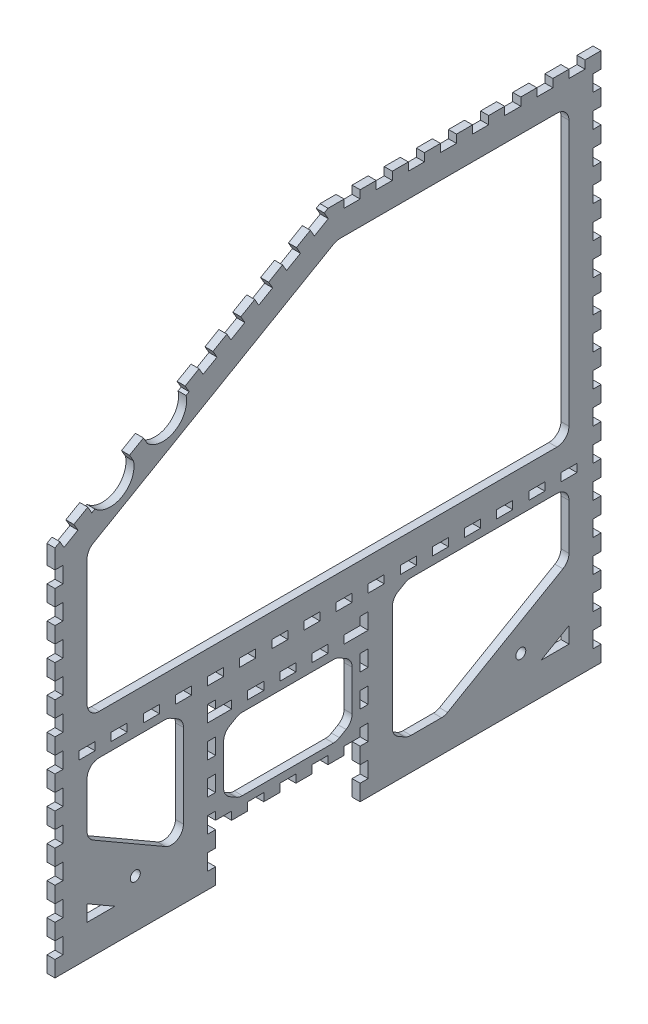
SolidWorks part; units mm, degrees
material "Pine"
ref_plane "Front Plane" through (0, 0, 0) normal (0, 0, 1) x (1, 0, 0)
ref_plane "Top Plane" through (0, 0, 0) normal (0, 1, 0) x (1, 0, 0)
ref_plane "Right Plane" through (0, 0, 0) normal (1, 0, 0) x (0, 0, -1)
sketch "Sketch2" plane through (0, 0, 0) normal (1, 0, 0) x (0, 0, -1)
  line L0 (0, 0) -> (0, 294.4501)
  line L1 (0, 294.4501) -> (215.9, 419.1)
  line L2 (215.9, 419.1) -> (431.8, 419.1)
  line L3 (431.8, 419.1) -> (431.8, 0)
  line L4 (431.8, 0) -> (241.3, 0)
  line L5 (241.3, 0) -> (241.3, 38.1)
  line L6 (241.3, 38.1) -> (127, 38.1)
  line L7 (127, 38.1) -> (127, 0)
  line L8 (127, 0) -> (0, 0)
  dimension "D1" = 431.8
  dimension "D2" = 419.1
  dimension "D3" = 127
  dimension "D4" = 114.3
  dimension "D5" = 38.1
  dimension "D6" = 215.9
  dimension "D7" = 150
extrude "Boss-Extrude1" add sketch "Sketch2" along normal blind 6.35 contours L1 L2 L3 L4 L5 L6 L7 L8 L0
sketch "Sketch3" plane through (6.35, 0, 0) normal (1, 0, 0) x (0, 0, -1)
  line L0 (0, 38.1) -> (431.8, 38.1) construction
  line L1 (0, 0) -> (0, 294.4501) construction
  line L2 (431.8, 419.1) -> (431.8, 0) construction
  circle A0 centre (63.5, 38.1) radius 3.9687
  circle A1 centre (368.3, 38.1) radius 3.9688
  dimension "D4" = 7.9375
  dimension "D5" = 7.9375
  dimension "D1" = 38.1
  dimension "D2" = 63.5
  dimension "D3" = 63.5
extrude "Cut-Extrude1" cut sketch "Sketch3" against normal through all
sketch "Sketch4" plane through (6.35, 0, 0) normal (1, 0, 0) x (0, 0, -1)
  line L0 (431.8, 419.1) -> (431.8, 0) construction
  line L1 (215.9, 419.1) -> (431.8, 419.1) construction
  line L2 (393.7, 400.05) -> (393.7, 19.05) construction
  line L4 (393.7, 400.05) -> (330.2, 400.05) construction
  line L5 (330.2, 400.05) -> (330.2, 19.05) construction
  line L6 (330.2, 400.05) -> (330.2, 19.05) construction
  line L7 (330.2, 400.05) -> (323.5506, 19.108) construction
  circle A0 centre (393.7, 400.05) radius 3.175 construction
  circle A1 centre (393.7, 19.05) radius 3.175 construction
  circle A2 centre (323.5506, 19.108) radius 3.175 construction
  circle A3 centre (316.9033, 19.2821) radius 3.175 construction
  circle A4 centre (330.2, 400.05) radius 3.175 construction
  circle A5 centre (330.2, 19.05) radius 3.175 construction
  circle A6 centre (310.26, 19.5721) radius 3.175 construction
  circle A7 centre (303.6228, 19.9781) radius 3.175 construction
  circle A8 centre (296.9937, 20.4998) radius 3.175 construction
  circle A9 centre (290.3747, 21.1372) radius 3.175 construction
  circle A10 centre (283.7678, 21.8899) radius 3.175 construction
  circle A11 centre (277.175, 22.7579) radius 3.175 construction
  circle A12 centre (270.5985, 23.7407) radius 3.175 construction
  dimension "D1" = 6.35
  dimension "D2" = 38.1
  dimension "D3" = 19.05
  dimension "D4" = 381
  dimension "D5" = 10
  dimension "D6" = 1
  dimension "D7" = 101.6
sketch "Sketch5" plane through (6.35, 0, 0) normal (1, 0, 0) x (0, 0, -1)
  line L0 (431.8, 419.1) -> (431.8, 0) construction
  line L1 (431.8, 12.7) -> (425.45, 12.7)
  line L2 (431.8, 12.7) -> (431.8, 25.4)
  line L3 (431.8, 25.4) -> (425.45, 25.4)
  line L4 (425.45, 12.7) -> (425.45, 25.4)
  line L5 (431.8, 0) -> (241.3, 0) construction
  dimension "D1" = 6.35
  dimension "D2" = 12.7
  dimension "D3" = 12.7
extrude "Cut-Extrude3" cut sketch "Sketch5" against normal through all
pattern_linear "LPattern1" count 16 spacing 25.4 along (0, 1, 0) of "Cut-Extrude3"
sketch "Sketch6" plane through (6.35, 0, 0) normal (1, 0, 0) x (0, 0, -1)
  line L0 (0, 0) -> (0, 294.4501) construction
  line L1 (0, 12.7) -> (6.35, 12.7)
  line L2 (0, 12.7) -> (0, 25.4)
  line L3 (0, 25.4) -> (6.35, 25.4)
  line L4 (6.35, 12.7) -> (6.35, 25.4)
  line L5 (425.45, 12.7) -> (431.8, 12.7) construction
  line L6 (425.45, 25.4) -> (425.45, 12.7) construction
  line L7 (127, 0) -> (0, 0) construction
  dimension "D1" = 12.7
extrude "Cut-Extrude4" cut sketch "Sketch6" against normal through all
pattern_linear "LPattern2" count 11 spacing 25.4 along (0, 1, 0) of "Cut-Extrude4"
sketch "Sketch7" plane through (6.35, 0, 0) normal (1, 0, 0) x (0, 0, -1)
  line L0 (127, 38.1) -> (127, 0) construction
  line L1 (127, 12.7) -> (120.65, 12.7)
  line L2 (127, 12.7) -> (127, 25.4)
  line L3 (127, 25.4) -> (120.65, 25.4)
  line L4 (120.65, 12.7) -> (120.65, 25.4)
  line L5 (241.3, 38.1) -> (127, 38.1) construction
  line L6 (127, 38.1) -> (139.7, 38.1)
  line L7 (127, 38.1) -> (127, 44.45)
  line L8 (127, 44.45) -> (139.7, 44.45)
  line L9 (139.7, 38.1) -> (139.7, 44.45)
  line L10 (241.3, 0) -> (241.3, 38.1) construction
  line L11 (152.4, 38.1) -> (165.1, 38.1)
  line L12 (152.4, 38.1) -> (152.4, 44.45)
  line L13 (152.4, 44.45) -> (165.1, 44.45)
  line L14 (165.1, 38.1) -> (165.1, 44.45)
  line L15 (177.8, 38.1) -> (190.5, 38.1)
  line L16 (177.8, 38.1) -> (177.8, 44.45)
  line L17 (177.8, 44.45) -> (190.5, 44.45)
  line L18 (190.5, 38.1) -> (190.5, 44.45)
  line L19 (241.3, 25.4) -> (247.65, 25.4)
  line L20 (241.3, 25.4) -> (241.3, 12.7)
  line L21 (241.3, 12.7) -> (247.65, 12.7)
  line L22 (247.65, 25.4) -> (247.65, 12.7)
  line L23 (0, 12.7) -> (6.35, 12.7) construction
  line L24 (6.35, 12.7) -> (6.35, 25.4) construction
  line L25 (127, 0) -> (0, 0) construction
  line L26 (431.8, 0) -> (241.3, 0) construction
  line L27 (203.2, 44.45) -> (215.9, 44.45)
  line L28 (203.2, 44.45) -> (203.2, 38.1)
  line L29 (203.2, 38.1) -> (215.9, 38.1)
  line L30 (215.9, 44.45) -> (215.9, 38.1)
  line L32 (241.3, 38.1) -> (228.6, 38.1)
  line L33 (241.3, 38.1) -> (241.3, 44.45)
  line L34 (241.3, 44.45) -> (228.6, 44.45)
  line L35 (228.6, 38.1) -> (228.6, 44.45)
  dimension "D1" = 12.7
  dimension "D2" = 12.7
  dimension "D4" = 12.7
  dimension "D5" = 12.7
  dimension "D6" = 12.7
extrude "Cut-Extrude5" cut sketch "Sketch7" against normal through all
sketch "Sketch8" plane through (6.35, 0, 0) normal (1, 0, 0) x (0, 0, -1)
  line L0 (201.9351, 411.0373) -> (212.9336, 417.3873)
  line L1 (201.9351, 411.0373) -> (205.1101, 405.5381)
  line L2 (212.9336, 417.3873) -> (216.1086, 411.8881)
  line L3 (205.1101, 405.5381) -> (216.1086, 411.8881)
  line L4 (0, 294.4501) -> (215.9, 419.1) construction
  line L5 (6.35, 279.4) -> (0, 279.4) construction
  line L6 (6.35, 266.7) -> (6.35, 279.4) construction
  line L7 (216.1086, 411.8881) -> (7.1367, 291.2381) construction
  line L8 (6.35, 279.4) -> (6.35, 292.1) construction
  line L9 (215.9, 412.75) -> (215.6832, 412.6248) construction
  line L10 (7.1367, 291.2381) -> (3.9617, 296.7373) construction
  line L11 (6.35, 292.1) -> (6.5668, 292.2252) construction
  line L12 (215.9, 419.1) -> (215.9, 412.75) construction
  line L13 (215.9, 419.1) -> (431.8, 419.1) construction
  dimension "D1" = 215.9
  dimension "D2" = 241.3
  dimension "D3" = 6.35
extrude "Cut-Extrude6" cut sketch "Sketch8" against normal through all
pattern_linear "LPattern3" count 10 spacing 25.4 along (0, -0.5, 0.866) of "Cut-Extrude6"
sketch "Sketch9" plane through (6.35, 0, 0) normal (1, 0, 0) x (0, 0, -1)
  line L0 (215.9, 419.1) -> (431.8, 419.1) construction
  line L1 (419.1, 419.1) -> (406.4, 419.1)
  line L2 (419.1, 419.1) -> (419.1, 412.75)
  line L3 (419.1, 412.75) -> (406.4, 412.75)
  line L4 (406.4, 419.1) -> (406.4, 412.75)
  line L5 (431.8, 406.4) -> (425.45, 406.4) construction
  line L6 (425.45, 406.4) -> (425.45, 393.7) construction
  line L7 (431.8, 419.1) -> (431.8, 406.4) construction
  dimension "D1" = 12.7
extrude "Cut-Extrude7" cut sketch "Sketch9" against normal through all
pattern_linear "LPattern4" count 8 spacing 25.4 along (0, 0, 1) of "Cut-Extrude7"
sketch "Sketch10" plane through (6.35, 0, 0) normal (1, 0, 0) x (0, 0, -1)
  line L0 (127, 0) -> (0, 0) construction
  line L1 (146.05, 273.05) -> (222.25, 273.05) construction
  line L2 (146.05, 273.05) -> (146.05, 57.15) construction
  line L3 (146.05, 57.15) -> (222.25, 57.15) construction
  line L4 (222.25, 273.05) -> (222.25, 57.15) construction
  line L5 (146.05, 273.05) -> (19.05, 273.05) construction
  line L6 (146.05, 273.05) -> (146.05, 247.65) construction
  line L7 (146.05, 247.65) -> (19.05, 247.65) construction
  line L8 (19.05, 273.05) -> (19.05, 247.65) construction
  line L9 (0, 254) -> (0, 266.7) construction
  line L10 (127, 44.45) -> (127, 25.4) construction
  line L11 (241.3, 25.4) -> (241.3, 44.45) construction
  line L12 (152.4, 38.1) -> (139.7, 38.1) construction
  circle A0 centre (222.25, 273.05) radius 3.175
  circle A1 centre (222.25, 57.15) radius 3.175
  circle A2 centre (146.05, 57.15) radius 3.175
  circle A3 centre (146.05, 273.05) radius 3.175
  circle A4 centre (19.05, 273.05) radius 3.175 construction
  circle A5 centre (19.05, 247.65) radius 3.175 construction
  circle A6 centre (146.05, 247.65) radius 3.175 construction
  dimension "D4" = 6.35
  dimension "D1" = 273.05
  dimension "D2" = 19.05
  dimension "D3" = 247.65
  dimension "D5" = 19.05
  dimension "D6" = 19.05
  dimension "D7" = 19.05
extrude "Cut-Extrude8" cut sketch "Sketch10" against normal through all
sketch "Sketch11" plane through (6.35, 0, 0) normal (1, 0, 0) x (0, 0, -1)
  line L0 (127, 0) -> (0, 0) construction
  line L1 (0, 254) -> (0, 266.7) construction
  line L5 (241.3, 0) -> (241.3, 12.7) construction
  line L6 (177.8, 38.1) -> (165.1, 38.1) construction
  line L7 (38.1, 260.35) -> (266.7, 260.35) construction
  line L8 (266.7, 260.35) -> (266.7, 63.5) construction
  circle A0 centre (38.1, 260.35) radius 3.9688
  circle A1 centre (266.7, 63.5) radius 3.9688 construction
  circle A2 centre (266.7, 260.35) radius 3.9688
  dimension "D3" = 7.9375
  dimension "D1" = 260.35
  dimension "D2" = 38.1
  dimension "D4" = 25.4
  dimension "D5" = 25.4
extrude "Cut-Extrude9" cut sketch "Sketch11" against normal through all
sketch "Sketch12" plane through (6.35, 0, 0) normal (1, 0, 0) x (0, 0, -1)
  line L0 (127, 50.8) -> (127, 38.1)
  line L1 (120.65, 25.4) -> (127, 25.4)
  line L2 (120.65, 25.4) -> (120.65, 12.7)
  line L3 (120.65, 12.7) -> (127, 12.7)
  line L4 (127, 25.4) -> (127, 12.7)
  line L5 (120.65, 50.8) -> (127, 50.8)
  line L6 (120.65, 50.8) -> (120.65, 38.1)
  line L7 (120.65, 38.1) -> (127, 38.1)
  line L8 (127, 76.2) -> (127, 63.5)
  line L9 (120.65, 76.2) -> (127, 76.2)
  line L10 (120.65, 76.2) -> (120.65, 63.5)
  line L11 (120.65, 63.5) -> (127, 63.5)
  line L12 (127, 101.6) -> (127, 88.9)
  line L13 (120.65, 101.6) -> (127, 101.6)
  line L14 (120.65, 101.6) -> (120.65, 88.9)
  line L15 (120.65, 88.9) -> (127, 88.9)
  line L16 (127, 127) -> (127, 114.3)
  line L17 (120.65, 127) -> (127, 127)
  line L18 (120.65, 127) -> (120.65, 114.3)
  line L19 (120.65, 114.3) -> (127, 114.3)
  line L20 (127, 152.4) -> (127, 139.7) construction
  line L21 (120.65, 152.4) -> (127, 152.4) construction
  line L22 (120.65, 152.4) -> (120.65, 139.7) construction
  line L23 (120.65, 139.7) -> (127, 139.7) construction
  line L24 (127, 177.8) -> (127, 165.1) construction
  line L25 (120.65, 177.8) -> (127, 177.8) construction
  line L26 (120.65, 177.8) -> (120.65, 165.1) construction
  line L27 (120.65, 165.1) -> (127, 165.1) construction
  dimension "D1" = 7
extrude "Cut-Extrude13" cut sketch "Sketch12" against normal through all
sketch "Sketch13" plane through (6.35, 0, 0) normal (1, 0, 0) x (0, 0, -1)
  line L1 (120.65, 25.4) -> (120.65, 12.7) construction
  line L2 (84.65, 117.2) -> (347.15, 117.2) construction
  line L3 (84.65, 117.2) -> (6.35, 117.2) construction
  line L4 (6.35, 114.3) -> (6.35, 127) construction
  line L5 (347.15, 117.2) -> (425.45, 117.2) construction
  line L6 (425.45, 127) -> (425.45, 114.3) construction
  circle A0 centre (84.65, 117.2) radius 20
  circle A1 centre (347.15, 117.2) radius 20
  dimension "D2" = 40
  dimension "D1" = 9.8
  dimension "D3" = 36
sketch "Sketch14" plane through (6.35, 0, 0) normal (1, 0, 0) x (0, 0, -1)
  line L0 (36.9572, 315.7873) -> (47.9558, 322.1373)
  line L1 (36.9572, 315.7873) -> (40.1322, 310.2881)
  line L2 (47.9558, 322.1373) -> (51.1308, 316.6381)
  line L3 (40.1322, 310.2881) -> (51.1308, 316.6381)
  line L4 (80.9513, 341.1873) -> (91.9498, 347.5373)
  line L5 (80.9513, 341.1873) -> (84.1263, 335.6881)
  line L6 (91.9498, 347.5373) -> (95.1248, 342.0381)
  line L7 (84.1263, 335.6881) -> (95.1248, 342.0381)
  line L8 (91.9498, 347.5373) -> (95.1248, 342.0381) construction
extrude "Cut-Extrude15" cut sketch "Sketch14" against normal through all
sketch "Sketch15" plane through (6.35, 0, 0) normal (1, 0, 0) x (0, 0, -1)
  line L0 (43.8866, 319.2853) -> (85.4558, 343.2853) construction
  line L1 (46.8439, 314.1631) -> (53.1939, 303.1646) construction
  line L3 (64.6712, 331.2853) -> (64.4535, 331.6623) construction
  line L4 (58.9543, 328.4873) -> (69.9528, 334.8373) construction
  line L5 (29.1337, 303.9381) -> (62.1293, 322.9881) construction
  line L6 (31.5586, 305.3381) -> (62.1293, 322.9881)
  line L7 (73.1278, 329.3381) -> (103.6985, 346.9881)
  line L8 (73.1278, 329.3381) -> (106.1234, 348.3881) construction
  circle A0 centre (43.8866, 319.2853) radius 18.6147
  circle A1 centre (85.4558, 343.2853) radius 18.6147
  dimension "D2" = 12.7
  dimension "D1" = 48
extrude "Cut-Extrude16" cut sketch "Sketch15" against normal through all contours L6 A0 | L7 A1
sketch "Sketch17" plane through (6.35, 0, 0) normal (1, 0, 0) x (0, 0, -1)
  line L0 (0, 139.7) -> (6.35, 139.7) construction
  line L1 (19.05, 146.05) -> (31.75, 146.05)
  line L2 (19.05, 146.05) -> (19.05, 139.7)
  line L3 (19.05, 139.7) -> (31.75, 139.7)
  line L4 (31.75, 146.05) -> (31.75, 139.7)
  line L5 (6.35, 139.7) -> (6.35, 152.4) construction
  dimension "D1" = 12.7
  dimension "D2" = 6.35
  dimension "D3" = 12.7
extrude "Cut-Extrude17" cut sketch "Sketch17" against normal through all
pattern_linear "LPattern5" count 17 spacing 25.4 along (0, 0, -1) of "Cut-Extrude17"
pattern_linear "LPattern6" count 2 spacing 120.65 along (0, 0, -1) of "Cut-Extrude13"
sketch "Sketch18" plane through (6.35, 0, 0) normal (1, 0, 0) x (0, 0, -1)
  line L1 (127, 120.65) -> (139.7, 120.65)
  line L2 (127, 120.65) -> (127, 114.3)
  line L3 (127, 114.3) -> (139.7, 114.3)
  line L4 (139.7, 120.65) -> (139.7, 114.3)
  dimension "D1" = 12.7
  dimension "D2" = 6.35
extrude "Cut-Extrude18" cut sketch "Sketch18" against normal through all
pattern_linear "LPattern7" count 5 spacing 25.4 along (0, 0, -1) of "Cut-Extrude18"
sketch "Sketch19" plane through (6.35, 0, 0) normal (1, 0, 0) x (0, 0, -1)
  line L0 (25.4, 279.7854) -> (222.7059, 393.7)
  line L1 (222.7059, 393.7) -> (406.4, 393.7)
  line L2 (406.4, 393.7) -> (406.4, 165.1)
  line L3 (406.4, 165.1) -> (25.4, 165.1)
  line L4 (25.4, 165.1) -> (25.4, 279.7854)
  line L5 (0, 228.6) -> (0, 241.3) construction
  line L6 (431.8, 292.1) -> (431.8, 279.4) construction
  line L7 (368.3, 419.1) -> (381, 419.1) construction
  line L9 (146.9425, 379.2873) -> (157.941, 385.6373) construction
  line L10 (124.9454, 366.5873) -> (135.9439, 372.9373) construction
  line L11 (222.25, 139.7) -> (234.95, 139.7) construction
  point P16 (130.4447, 369.7623)
  dimension "D1" = 25.4
  dimension "D2" = 25.4
  dimension "D3" = 25.4
  dimension "D4" = 25.4
  dimension "D5" = 25.4
extrude "Cut-Extrude19" cut sketch "Sketch19" against normal through all
sketch "Sketch20" plane through (6.35, 0, 0) normal (1, 0, 0) x (0, 0, -1)
  line L0 (165.1, 120.65) -> (152.4, 120.65) construction
  line L1 (133.35, 107.95) -> (234.95, 107.95)
  line L2 (133.35, 107.95) -> (133.35, 50.8)
  line L3 (133.35, 50.8) -> (234.95, 50.8)
  line L4 (234.95, 107.95) -> (234.95, 50.8)
  line L5 (120.65, 101.6) -> (120.65, 88.9) construction
  line L6 (177.8, 38.1) -> (165.1, 38.1) construction
  line L7 (247.65, 101.6) -> (247.65, 88.9) construction
  dimension "D1" = 12.7
  dimension "D2" = 12.7
  dimension "D3" = 12.7
  dimension "D4" = 12.7
extrude "Cut-Extrude20" cut sketch "Sketch20" against normal through all
sketch "Sketch21" plane through (6.35, 0, 0) normal (1, 0, 0) x (0, 0, -1)
  line L0 (266.7, 25.4) -> (308.203, 25.4)
  line L1 (25.4, 133.35) -> (25.4, 82.0941)
  line L2 (308.203, 25.4) -> (406.4, 82.0941)
  line L3 (25.4, 82.0941) -> (101.6, 38.1)
  line L4 (406.4, 82.0941) -> (406.4, 133.35)
  line L5 (406.4, 133.35) -> (266.7, 133.35)
  line L6 (266.7, 133.35) -> (266.7, 25.4)
  line L7 (406.4, 165.1) -> (406.4, 393.7) construction
  line L8 (431.8, 0) -> (241.3, 0) construction
  line L9 (241.3, 25.4) -> (241.3, 38.1) construction
  line L10 (387.35, 146.05) -> (374.65, 146.05) construction
  line L11 (101.6, 38.1) -> (101.6, 133.35)
  line L12 (101.6, 133.35) -> (25.4, 133.35)
  line L13 (0, 101.6) -> (0, 114.3) construction
  line L14 (127, 101.6) -> (127, 88.9) construction
  line L20 (25.4, 38.1) -> (25.4, 25.4)
  line L21 (25.4, 25.4) -> (47.397, 25.4)
  line L22 (47.397, 25.4) -> (25.4, 38.1)
  circle A0 centre (63.5, 38.1) radius 3.9687 construction
  circle A1 centre (368.3, 38.1) radius 3.9688 construction
  dimension "D4" = 150
  dimension "D5" = 19.05
  dimension "D9" = 19.05
  dimension "D1" = 25.4
  dimension "D2" = 25.4
  dimension "D3" = 12.7
  dimension "D6" = 25.4
  dimension "D7" = 25.4
  dimension "D8" = 120
  dimension "D12" = 19.05
extrude "Cut-Extrude21" cut sketch "Sketch21" against normal through all
sketch "Sketch22" plane through (6.35, 0, 0) normal (1, 0, 0) x (0, 0, -1)
  line L0 (384.403, 25.4) -> (406.4, 38.1)
  line L1 (406.4, 38.1) -> (406.4, 25.4)
  line L2 (406.4, 25.4) -> (384.403, 25.4)
  line L3 (406.4, 82.0941) -> (406.4, 133.35) construction
  line L4 (266.7, 25.4) -> (308.203, 25.4) construction
  line L5 (358.775, 54.5978) -> (377.825, 21.6022) construction
  line L6 (308.203, 25.4) -> (406.4, 82.0941) construction
  point P11 (368.3, 38.1)
extrude "Cut-Extrude22" cut sketch "Sketch22" against normal through all
sketch "Sketch26" plane through (6.35, 0, 0) normal (1, 0, 0) x (0, 0, -1)
  line L0 (278.9441, 133.35) -> (234.95, 107.95) construction
  line L1 (278.9441, 133.35) -> (275.7691, 138.8493) construction
  line L2 (234.95, 107.95) -> (231.775, 113.4493) construction
  line L3 (275.7691, 138.8493) -> (231.775, 113.4493) construction
  line L4 (406.4, 133.35) -> (266.7, 133.35) construction
  line L5 (228.6, 120.65) -> (228.6, 114.3) construction
  line L6 (308.203, 25.4) -> (406.4, 82.0941) construction
  line L7 (266.7, 133.35) -> (266.7, 126.2809)
  line L8 (266.7, 133.35) -> (266.7, 25.4) construction
  line L9 (266.7, 126.2809) -> (278.9441, 133.35)
  line L10 (278.9441, 133.35) -> (266.7, 133.35)
  line L11 (89.3559, 133.35) -> (101.6, 126.2809)
  line L12 (101.6, 133.35) -> (25.4, 133.35) construction
  line L13 (101.6, 38.1) -> (101.6, 133.35) construction
  line L14 (101.6, 126.2809) -> (101.6, 133.35)
  line L15 (101.6, 133.35) -> (89.3559, 133.35)
  line L16 (25.4, 82.0941) -> (101.6, 38.1) construction
  line L17 (266.7, 32.4691) -> (278.9441, 25.4)
  line L18 (266.7, 133.35) -> (266.7, 25.4) construction
  line L19 (266.7, 25.4) -> (308.203, 25.4) construction
  line L20 (278.9441, 25.4) -> (266.7, 25.4)
  line L21 (266.7, 25.4) -> (266.7, 32.4691)
  line L22 (133.35, 107.95) -> (133.35, 100.8809)
  line L23 (133.35, 107.95) -> (133.35, 50.8) construction
  line L24 (133.35, 100.8809) -> (145.5941, 107.95)
  line L25 (234.95, 107.95) -> (133.35, 107.95) construction
  line L26 (145.5941, 107.95) -> (133.35, 107.95)
  line L27 (234.95, 107.95) -> (222.7059, 107.95)
  line L28 (222.7059, 107.95) -> (234.95, 100.8809)
  line L29 (234.95, 50.8) -> (234.95, 107.95) construction
  line L30 (234.95, 100.8809) -> (234.95, 107.95)
  line L31 (133.35, 50.8) -> (145.5941, 50.8)
  line L32 (133.35, 50.8) -> (234.95, 50.8) construction
  line L33 (145.5941, 50.8) -> (133.35, 57.8691)
  line L34 (133.35, 57.8691) -> (133.35, 50.8)
  line L35 (234.95, 50.8) -> (222.7059, 50.8)
  line L36 (222.7059, 50.8) -> (234.95, 57.8691)
  line L37 (234.95, 57.8691) -> (234.95, 50.8)
extrude "Boss-Extrude4" add sketch "Sketch26" against normal through all
fillet "Fillet1" radius 9.525 25 edges at (3.175, 133.35, -25.4) (3.175, 82.0941, -25.4) (3.175, 57.8691, -234.95) (3.175, 50.8, -222.7059) (3.175, 38.1, -101.6) (3.175, 50.8, -145.5941) (3.175, 57.8691, -133.35) (3.175, 100.8809, -133.35) (3.175, 126.2809, -101.6) (3.175, 133.35, -89.3559) (3.175, 107.95, -145.5941) (3.175, 100.8809, -234.95) (3.175, 107.95, -222.7059) (3.175, 133.35, -406.4) (3.175, 133.35, -278.9441) (3.175, 126.2809, -266.7) (3.175, 25.4, -308.203) (3.175, 32.4691, -266.7) (3.175, 25.4, -278.9441) (3.175, 82.0941, -406.4) (3.175, 165.1, -406.4) (3.175, 165.1, -25.4) (3.175, 279.7854, -25.4) (3.175, 393.7, -406.4) (3.175, 393.7, -222.7059)
